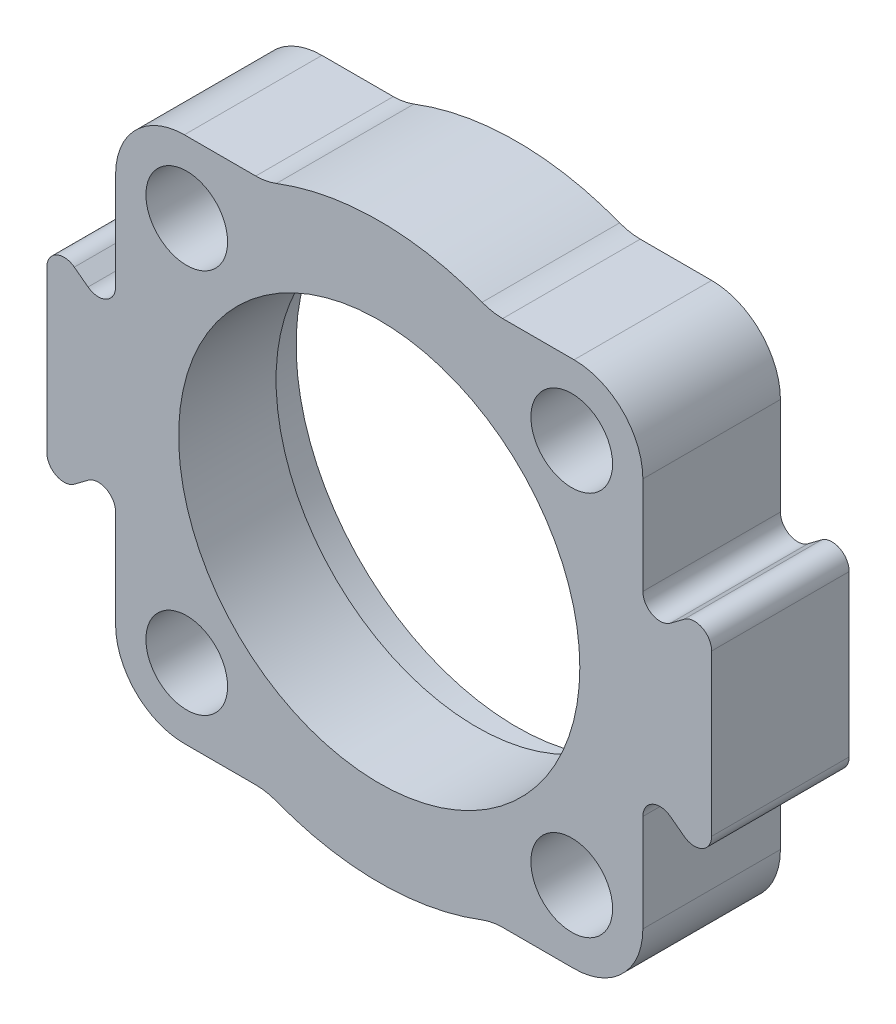
SolidWorks part; units mm, degrees
ref_plane "Front" through (0, 0, 0) normal (0, 0, 1) x (1, 0, 0)
ref_plane "Top" through (0, 0, 0) normal (0, 1, 0) x (1, 0, 0)
ref_plane "Right" through (0, 0, 0) normal (1, 0, 0) x (0, 0, -1)
sketch "Sketch1" plane through (0, 0, 0) normal (0, 0, 1) x (1, 0, 0)
  line L0 (-25.5577, 0) -> (87.0392, 0) construction
  line L1 (0, 61.8389) -> (0, -65.4134) construction
  line L2 (34, 46) -> (21.5407, 46)
  line L3 (46, 34) -> (46, 17)
  line L4 (58, 14) -> (58, -14)
  line L5 (0, 0) -> (79.5402, 79.5402) construction
  line L6 (46, -34) -> (46, -17)
  line L7 (34, -46) -> (21.5407, -46)
  line L8 (-34, -46) -> (-21.5407, -46)
  line L9 (-46, -34) -> (-46, -17)
  line L10 (-58, 14) -> (-58, -14)
  line L11 (-46, 34) -> (-46, 17)
  line L12 (-34, 46) -> (-21.5407, 46)
  line L13 (50.8, 14.6) -> (53.2, 16.4)
  line L14 (55, 17) -> (39.6052, 17) construction
  line L15 (50.8, -14.6) -> (53.2, -16.4)
  line L16 (-50.8, -14.6) -> (-53.2, -16.4)
  line L17 (-50.8, 14.6) -> (-53.2, 16.4)
  circle A0 centre (0, 0) radius 31
  arc A1 (17.9505, 46.6667) -> (-17.9505, 46.6667) centre (0, 0) ccw
  arc A2 (46, 17) -> (50.8, 14.6) centre (49, 17) ccw
  arc A3 (53.2, 16.4) -> (58, 14) centre (55, 14) cw
  circle A4 centre (0, 0) radius 47.5 construction
  circle A5 centre (33.5876, 33.5876) radius 7.125 construction
  arc A6 (46, 34) -> (34, 46) centre (34, 34) ccw
  arc A7 (17.9505, 46.6667) -> (21.5407, 46) centre (21.5407, 56) ccw
  arc A8 (17.9505, -46.6667) -> (21.5407, -46) centre (21.5407, -56) cw
  arc A9 (46, -34) -> (34, -46) centre (34, -34) cw
  circle A10 centre (33.5876, -33.5876) radius 7.125 construction
  arc A11 (53.2, -16.4) -> (58, -14) centre (55, -14) ccw
  arc A12 (46, -17) -> (50.8, -14.6) centre (49, -17) cw
  arc A13 (17.9505, -46.6667) -> (-17.9505, -46.6667) centre (0, 0) cw
  arc A14 (-46, -17) -> (-50.8, -14.6) centre (-49, -17) ccw
  arc A15 (-53.2, -16.4) -> (-58, -14) centre (-55, -14) cw
  circle A16 centre (-33.5876, -33.5876) radius 7.125 construction
  arc A17 (-46, -34) -> (-34, -46) centre (-34, -34) ccw
  arc A18 (-17.9505, -46.6667) -> (-21.5407, -46) centre (-21.5407, -56) ccw
  arc A19 (-17.9505, 46.6667) -> (-21.5407, 46) centre (-21.5407, 56) cw
  arc A20 (-46, 34) -> (-34, 46) centre (-34, 34) cw
  circle A21 centre (-33.5876, 33.5876) radius 7.125 construction
  arc A22 (-53.2, 16.4) -> (-58, 14) centre (-55, 14) ccw
  arc A23 (-46, 17) -> (-50.8, 14.6) centre (-49, 17) cw
  point P8 (-58, 0)
  point P38 (58, 0)
  dimension "D1" = 62
  dimension "D2" = 50
  dimension "D6" = 3
  dimension "D9" = 95
  dimension "D10" = 45
  dimension "D11" = 14.25
  dimension "D12" = 12
  dimension "D13" = 10
  dimension "D4" = 34
  dimension "D3" = 92
  dimension "D5" = 116
  dimension "D7" = 92
extrude "Base-Extrude" add sketch "Sketch1" along normal mid plane 25
sketch "Sketch2" plane through (0, 0, 0) normal (1, 0, 0) x (0, 0, -1)
  line L0 (0, 0) -> (40.5123, 0) construction
  line L1 (-12.5, 0) -> (12.5, 0) construction
  line L2 (11.5, 38.5) -> (4.5, 38.5)
  line L3 (-12.5, 34) -> (-12.5, 17) construction
  line L5 (4.5, 38.5) -> (4.5, 35)
  line L6 (4.5, 35) -> (-12.5, 35)
  line L7 (12.5, 70) -> (12.5, 0)
  line L8 (12.5, 0) -> (-12.5, 0)
  line L9 (-12.5, 0) -> (-12.5, 35)
  line L10 (11.5, 38.5) -> (11.5, 70)
  line L12 (11.5, 70) -> (12.5, 70)
  line L13 (12.5, 14) -> (12.5, -14) construction
  dimension "D1" = 7
  dimension "D2" = 24
  dimension "D3" = 70
  dimension "D4" = 77
  dimension "D5" = 70
revolve "Uddrejning" cut sketch "Sketch2" angle 360 about L0
sketch "Sketch4" plane through (0, 0, -11.5) normal (0, 0, 1) x (1, 0, 0)
  circle A0 centre (33.5876, 33.5876) radius 7.125 construction
  circle A1 centre (33.5876, -33.5876) radius 7.125 construction
  circle A2 centre (-33.5876, -33.5876) radius 7.125 construction
  circle A3 centre (-33.5876, 33.5876) radius 7.125 construction
  circle A4 centre (33.5876, 33.5876) radius 7.125
  circle A5 centre (33.5876, -33.5876) radius 7.125
  circle A6 centre (-33.5876, -33.5876) radius 7.125
  circle A7 centre (-33.5876, 33.5876) radius 7.125
extrude "4 stk ø14.25 huller" cut sketch "Sketch4" along normal through all
